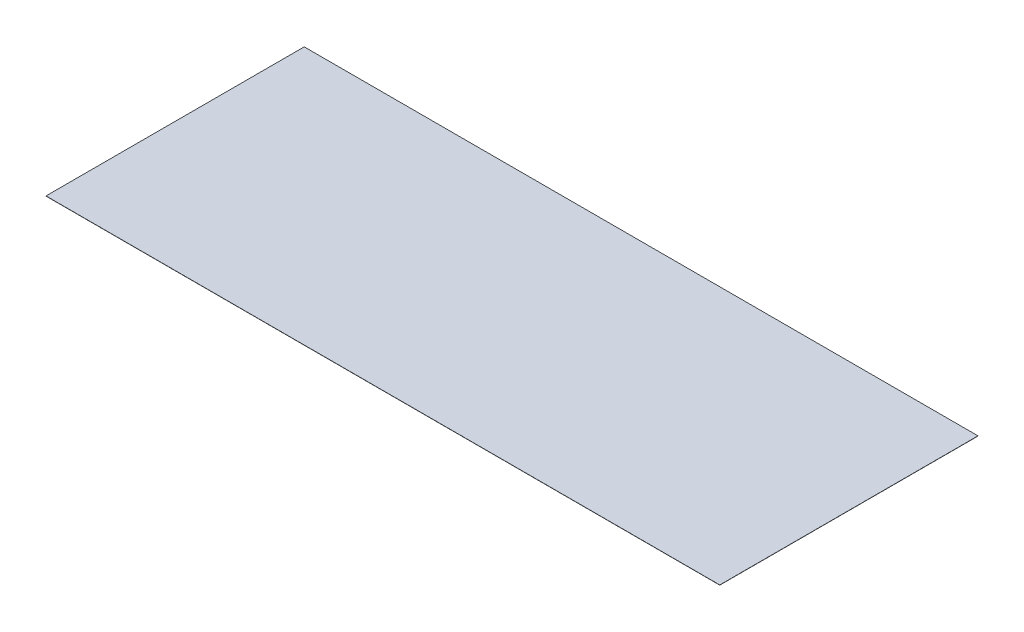
SolidWorks part; units mm, degrees
material "PE High Density Film"
ref_plane "Front Plane" through (0, 0, 0) normal (0, 0, 1) x (1, 0, 0)
ref_plane "Top Plane" through (0, 0, 0) normal (0, 1, 0) x (1, 0, 0)
ref_plane "Right Plane" through (0, 0, 0) normal (1, 0, 0) x (0, 0, -1)
sketch "Sketch1" plane through (0, 0, 0) normal (0, 1, 0) x (1, 0, 0)
  line L1 (-2743.2, -1051.306) -> (2743.2, -1051.306)
  line L2 (-2743.2, -1051.306) -> (-2743.2, 1051.306)
  line L3 (-2743.2, 1051.306) -> (2743.2, 1051.306)
  line L4 (2743.2, -1051.306) -> (2743.2, 1051.306)
  line L5 (-2743.2, -1051.306) -> (2743.2, 1051.306) construction
  line L6 (-2743.2, 1051.306) -> (2743.2, -1051.306) construction
  point P0 (0, 0)
  dimension "D1" = 2102.612
  dimension "D2" = 5486.4
extrude "Boss-Extrude1" add sketch "Sketch1" along normal blind 1.5875
